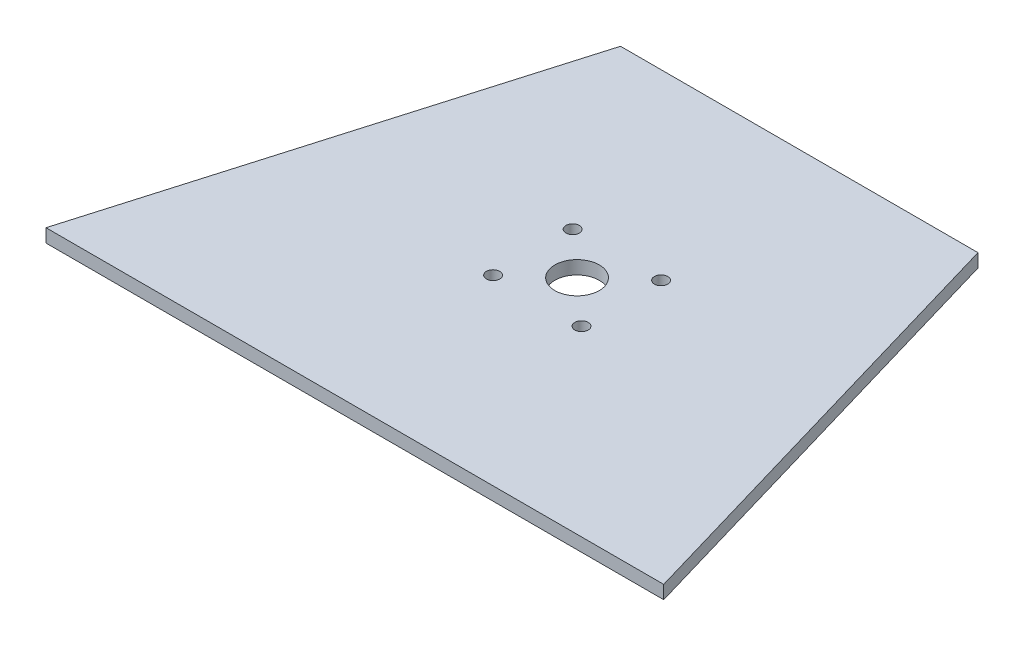
SolidWorks part; units mm, degrees
ref_plane "Front Plane" through (0, 0, 0) normal (0, 0, 1) x (1, 0, 0)
ref_plane "Top Plane" through (0, 0, 0) normal (0, 1, 0) x (1, 0, 0)
ref_plane "Right Plane" through (0, 0, 0) normal (1, 0, 0) x (0, 0, -1)
sketch "Sketch1" plane through (0, 0, 0) normal (0, 1, 0) x (1, 0, 0)
  line L0 (0, 0) -> (139, 0)
  line L1 (0, 0) -> (29.2799, 100)
  line L2 (139, 0) -> (109.7201, 100)
  line L3 (66.5, 0) -> (66.5, 100) construction
  line L4 (29.2799, 100) -> (109.7201, 100)
extrude "Boss-Extrude1" add sketch "Sketch1" along normal blind 3
hole_wizard "Ø10.0mm Dowel Hole1" positions "Sketch2" profile "Sketch3" hole size "Ø10.0" standard "ANSI Metric" end condition up to next
sketch "Sketch2" plane through (0, 3, 0) normal (0, 1, 0) x (1, 0, 0)
  point P0 (69.5, 50)
  point P4 (0, 0)
sketch "Sketch3" plane through (69.5, 3, -50) normal (1, 0, 0) x (0, 0, 1)
  line L0 (0, 0) -> (0, 3)
  line L1 (0, 3) -> (5, 3)
  line L2 (5, 3) -> (5, 0)
  line L5 (5, 0) -> (0, 0)
  line L11 (0, -6.35) -> (0, 107.95) construction
  dimension "Thru Hole Dia." = 10
  dimension "Thru Hole Depth" = 3
hole_wizard "Ø3.0mm Dowel Hole1" positions "Sketch4" profile "Sketch5" hole size "Ø3.0" standard "ANSI Metric" end condition up to next
sketch "Sketch4" plane through (0, 3, 0) normal (0, 1, 0) x (1, 0, 0)
  point P0 (59.55, 41.05)
  point P3 (59.55, 58.95)
  point P6 (79.45, 58.95)
  point P14 (79.45, 41.05)
  point P18 (0, 0)
sketch "Sketch5" plane through (59.55, 3, -41.05) normal (1, 0, 0) x (0, 0, 1)
  line L0 (0, 0) -> (0, 3)
  line L1 (0, 3) -> (1.5, 3)
  line L2 (1.5, 3) -> (1.5, 0)
  line L5 (1.5, 0) -> (0, 0)
  line L11 (0, -6.35) -> (0, 107.95) construction
  dimension "Thru Hole Dia." = 3
  dimension "Thru Hole Depth" = 3
